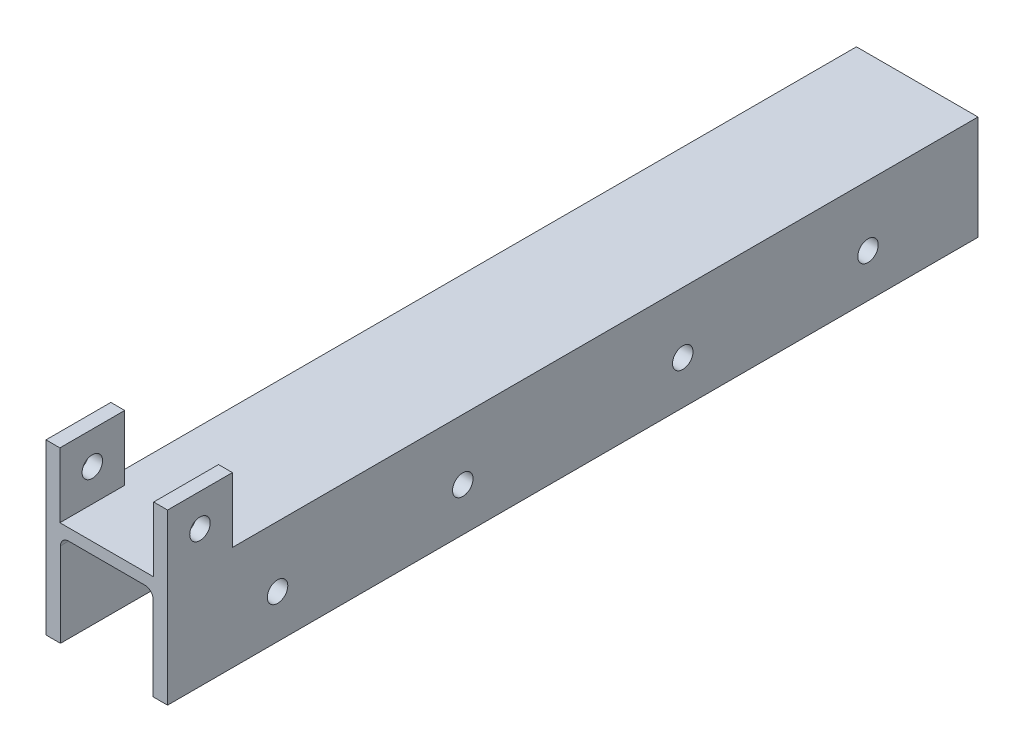
SolidWorks part; units mm, degrees
ref_plane "Front Plane" through (0, 0, 0) normal (0, 0, 1) x (1, 0, 0)
ref_plane "Top Plane" through (0, 0, 0) normal (0, 1, 0) x (1, 0, 0)
ref_plane "Right Plane" through (0, 0, 0) normal (1, 0, 0) x (0, 0, -1)
sketch "Sketch2" plane through (0, 0, 0) normal (0, 0, 1) x (1, 0, 0)
  line L0 (319.8414, 0) -> (-319.8414, 0) construction
  line L2 (0, 0) -> (0, 22.86)
  line L3 (0, 22.86) -> (26.67, 22.86)
  line L4 (26.67, 0) -> (26.67, 22.86)
  line L44 (23.495, 18.542) -> (23.495, 0)
  line L47 (3.175, 0) -> (3.175, 18.542)
  line L48 (4.953, 20.32) -> (21.717, 20.32)
  line L49 (0, 0) -> (3.175, 0)
  line L50 (23.495, 0) -> (26.67, 0)
  arc A0 (23.495, 18.542) -> (21.717, 20.32) centre (21.717, 18.542) ccw
  arc A1 (3.175, 18.542) -> (4.953, 20.32) centre (4.953, 18.542) cw
  point P15 (3.175, 20.32)
  point P16 (3.175, 20.32)
  dimension "D6" = 1.778
  dimension "D1" = 22.86
  dimension "D2" = 26.67
  dimension "D3" = 3.175
  dimension "D4" = 20.32
  dimension "D5" = 3.175
  dimension "D7" = 20.32
extrude "Boss-Extrude2" add sketch "Sketch2" against normal blind 177.8
sketch "Sketch19" plane through (0, 0, 0) normal (1, 0, 0) x (0, 0, -1)
  line L0 (0, 265.0009) -> (0, -265.0009) construction
  line L1 (319.8414, 0) -> (-319.8414, 0) construction
  line L2 (0, 20.32) -> (177.8, 20.32) construction
  line L3 (0, 0) -> (88.9, 0) construction
  line L4 (177.8, 0) -> (0, 0) construction
  line L5 (88.9, 0) -> (88.9, 22.86) construction
  line L6 (177.8, 22.86) -> (0, 22.86) construction
  line L7 (177.8, 0) -> (177.8, 22.86) construction
  circle A0 centre (24.13, 9.525) radius 2.2479
  circle A1 centre (64.77, 9.525) radius 2.2479
  circle A2 centre (113.03, 9.525) radius 2.2479
  circle A3 centre (153.67, 9.525) radius 2.2479
  dimension "D2" = 4.4958
  dimension "D5" = 4.4958
  dimension "D9" = 24.13
  dimension "D14" = 4.4958
  dimension "D1" = 24.13
  dimension "D3" = 9.525
  dimension "D4" = 40.64
  dimension "D6" = 9.525
  dimension "D7" = 24.13
  dimension "D8" = 88.9
  dimension "D10" = 40.64
  dimension "D11" = 24.13
  dimension "D12" = 2.54
  dimension "D13" = 20.32
extrude "Cut-Extrude3" cut sketch "Sketch19" along normal through all
sketch "Sketch21" plane through (0, 22.86, 0) normal (0, 1, 0) x (1, 0, 0)
  line L0 (13.335, 0) -> (13.335, 177.8) construction
  line L1 (0, 0) -> (26.67, 0) construction
  line L2 (0, 0) -> (3.048, 0)
  line L3 (0, 0) -> (0, 14.224)
  line L4 (0, 14.224) -> (3.048, 14.224)
  line L5 (3.048, 0) -> (3.048, 14.224)
  line L6 (26.67, 177.8) -> (0, 177.8) construction
  line L7 (0, 0) -> (6.096, 0) construction
  line L8 (6.096, 0) -> (6.096, 6.5548) construction
  line L10 (20.574, 0) -> (20.574, 6.5548) construction
  line L11 (26.67, 0) -> (23.622, 0)
  line L12 (26.67, 0) -> (26.67, 14.224)
  line L13 (26.67, 14.224) -> (23.622, 14.224)
  line L14 (23.622, 0) -> (23.622, 14.224)
  dimension "D1" = 6.096
  dimension "D2" = 6.096
  dimension "D3" = 14.224
  dimension "D4" = 14.478
  dimension "D5" = 3.048
  dimension "D6" = 3.048
  dimension "D7" = 14.224
extrude "Boss-Extrude4" add sketch "Sketch21" along normal blind 14.224
sketch "Sketch22" plane through (23.622, 0, 0) normal (-1, 0, 0) x (0, 0, 1)
  line L0 (0, 37.084) -> (-14.224, 37.084) construction
  line L1 (0, -265.0009) -> (0, 265.0009) construction
  line L2 (-14.224, 22.86) -> (0, 22.86) construction
  line L3 (-7.112, 22.86) -> (-7.112, 29.972) construction
  line L4 (-177.8, 0) -> (0, 0) construction
  circle A0 centre (-7.112, 29.972) radius 2.2479
  point P4 (-7.112, 37.084)
  dimension "D1" = 4.4958
  dimension "D2" = 7.112
  dimension "D3" = 7.112
  dimension "D4" = 14.224
  dimension "D5" = 7.112
  dimension "D6" = 29.972
extrude "Cut-Extrude4" cut sketch "Sketch22" against normal through all both and the other way through all
